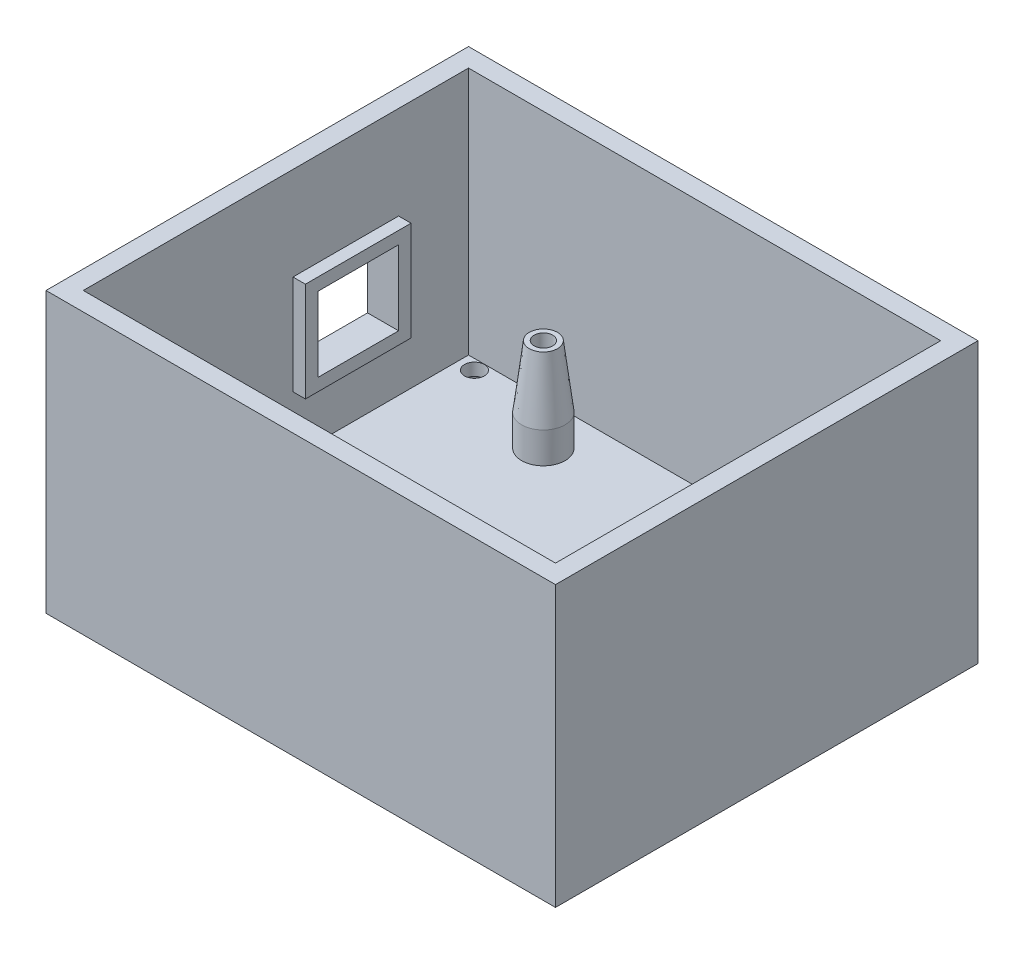
SolidWorks part; units mm, degrees
ref_plane "Спереди" through (0, 0, 0) normal (0, 0, 1) x (1, 0, 0)
ref_plane "Сверху" through (0, 0, 0) normal (0, 1, 0) x (1, 0, 0)
ref_plane "Справа" through (0, 0, 0) normal (1, 0, 0) x (0, 0, -1)
sketch "Sketch1" plane through (0, 0, 0) normal (0, 1, 0) x (1, 0, 0)
  line L1 (41, 34) -> (-41, 34)
  line L2 (41, 34) -> (41, -34)
  line L3 (41, -34) -> (-41, -34)
  line L4 (-41, 34) -> (-41, -34)
  line L5 (41, 34) -> (-41, -34) construction
  line L6 (41, -34) -> (-41, 34) construction
  point P0 (0, 0)
  dimension "D1" = 82
  dimension "D2" = 68
extrude "Boss-Extrude1" add sketch "Sketch1" along normal blind 5
sketch "Sketch2" plane through (0, 5, 0) normal (0, 1, 0) x (1, 0, 0)
  line L1 (-41, 34) -> (41, 34)
  line L2 (-41, 34) -> (-41, -34)
  line L3 (-41, -34) -> (41, -34)
  line L4 (41, 34) -> (41, -34)
  line L5 (-41, 34) -> (41, -34) construction
  line L6 (-41, -34) -> (41, 34) construction
  line L7 (-38, 31) -> (38, 31)
  line L8 (-38, 31) -> (-38, -31)
  line L9 (-38, -31) -> (38, -31)
  line L10 (38, 31) -> (38, -31)
  line L11 (-38, 31) -> (38, -31) construction
  line L12 (-38, -31) -> (38, 31) construction
  point P0 (0, 0)
  point P7 (0, 0)
  dimension "D1" = 3
  dimension "D2" = 3
  dimension "D3" = 76
  dimension "D4" = 62
  dimension "D5" = 82
  dimension "D6" = 68
extrude "Boss-Extrude2" add sketch "Sketch2" along normal blind 40
sketch "Эскиз1" plane through (0, 5, 0) normal (0, 1, 0) x (1, 0, 0)
  line L0 (-34.3, 26.65) -> (34.3, 26.65) construction
  line L1 (34.3, -26.65) -> (-34.3, 26.65) construction
  line L2 (-34.3, -26.65) -> (34.3, 26.65) construction
  line L5 (31.8, -24.15) -> (-34.3, -24.15) construction
  line L7 (34.3, 26.65) -> (34.3, -26.65) construction
  line L8 (34.3, -26.65) -> (-34.3, -26.65) construction
  line L9 (-34.3, -26.65) -> (-34.3, 26.65) construction
  line L10 (-34.3, 26.65) -> (-20.3, 26.65) construction
  line L11 (31.8, 26.65) -> (31.8, 8.85) construction
  line L12 (31.8, 8.85) -> (31.8, 24.05) construction
  line L13 (-20.3, 26.65) -> (-19, 26.65) construction
  line L14 (-20.3, 26.65) -> (-20.3, -26.65) construction
  line L15 (-19, 26.65) -> (31.8, 26.65) construction
  line L16 (31.8, 26.65) -> (31.8, -26.65) construction
  line L17 (31.8, -26.65) -> (31.8, -24.15) construction
  line L18 (31.8, 24.05) -> (-19, 24.05) construction
  line L19 (-19, 26.65) -> (-19, -26.65) construction
  circle A0 centre (31.8, -19.05) radius 1.5
  circle A1 centre (-20.3, -24.15) radius 1.5
  circle A2 centre (31.8, 8.85) radius 1.5
  circle A3 centre (-19, 24.05) radius 1.5
  circle A4 centre (-20.3, -24.15) radius 3.5
  circle A5 centre (-19, 24.05) radius 3.5
  circle A6 centre (31.8, 8.85) radius 3.5
  circle A7 centre (31.8, -19.05) radius 3.5
  point P0 (0, 0)
  point P3 (0, 0)
  point P6 (3.1764, 2.4705)
  point P11 (-20.3, -24.15)
  dimension "D12" = 3
  dimension "D2" = 7
  dimension "D4" = 68.6
  dimension "D5" = 14
  dimension "D6" = 1.3
  dimension "D7" = 50.8
  dimension "D8" = 2.5
  dimension "D9" = 5.1
  dimension "D10" = 27.9
  dimension "D11" = 15.2
extrude "Boss-Extrude3" add sketch "Эскиз1" along normal blind 15
sketch "Sketch4" plane through (-41, 0, 0) normal (-1, 0, 0) x (0, 0, 1)
  line L0 (0, 45) -> (0, 0) construction
  line L1 (-17.75, 28) -> (-4.75, 28)
  line L2 (-17.75, 45) -> (-17.75, 16) construction
  line L3 (-34, 0) -> (34, 0) construction
  line L4 (-4.75, 16) -> (-4.75, 45) construction
  line L5 (26.75, 16) -> (-26.75, 16) construction
  line L6 (-34, 45) -> (34, 45) construction
  line L7 (-17.75, 28) -> (-17.75, 16)
  line L8 (-17.75, 16) -> (-4.75, 16)
  line L10 (-4.75, 16) -> (-4.75, 28)
  point P7 (0, 16)
  point P8 (-11.25, 16)
  dimension "D1" = 53.5
  dimension "D2" = 29
  dimension "D3" = 13
  dimension "D4" = 12
extrude "Cut-Extrude1" cut sketch "Sketch4" against normal up to surface (3 mm away) up to face at (-38, 25, 0)
sketch "Sketch5" plane through (0, 0, 0) normal (0, -1, 0) x (1, 0, 0)
  line L0 (-41, 0) -> (41, 0) construction
  line L1 (-41, -34) -> (-41, 34) construction
  line L2 (41, 34) -> (41, -34) construction
  circle A0 centre (-20, 0) radius 1.6
  circle A1 centre (20, 0) radius 1.6
  dimension "D1" = 40
  dimension "D3" = 3.2
  dimension "D2" = 20
extrude "Cut-Extrude2" cut sketch "Sketch5" against normal through all
sketch "Sketch6" plane through (0, 0, -34) normal (0, 0, -1) x (-1, 0, 0)
  line L0 (-41, 15) -> (41, 15) construction
  line L1 (-41, 45) -> (-41, 0) construction
  line L2 (41, 45) -> (41, 0) construction
  line L3 (-41, 7) -> (41, 7) construction
  line L4 (-41, 0) -> (41, 0) construction
  text T0 "<b>SIMCHAIR MK III</b>" font "Arial Narrow" height 16
  text T1 "<b>I2C EDITION</b>" font "Arial Narrow" height 6
  dimension "D1" = 15
  dimension "D2" = 7
extrude "Boss-Extrude4" add sketch "Sketch6" along normal blind 1
sketch "Sketch7" plane through (0, 0, 0) normal (0, -1, 0) x (1, 0, 0)
  line L0 (-41, -34) -> (41, 34) construction
  line L1 (41, -34) -> (-41, 34) construction
  line L2 (35.4089, -29.3635) -> (-35.4089, -29.3635) construction
  line L3 (-35.4089, -29.3635) -> (-35.4089, 29.3635) construction
  line L4 (-35.4089, 29.3635) -> (35.4089, 29.3635) construction
  line L5 (35.4089, 29.3635) -> (35.4089, -29.3635) construction
  circle A0 centre (35.4089, -29.3635) radius 1.6
  circle A1 centre (-35.4089, -29.3635) radius 1.6
  circle A2 centre (-35.4089, 29.3635) radius 1.6
  circle A3 centre (35.4089, 29.3635) radius 1.6
  dimension "D2" = 3.2
  dimension "D1" = 92
extrude "Cut-Extrude3" cut sketch "Sketch7" against normal through all
sketch "Sketch8" plane through (0, 0, 0) normal (0, -1, 0) x (1, 0, 0)
  line L0 (-41, 34) -> (41, 34) construction
  line L1 (33.7839, 26.5489) -> (37.0339, 26.5489)
  line L2 (37.0339, 26.5489) -> (38.6589, 29.3635)
  line L3 (38.6589, 29.3635) -> (37.0339, 32.178)
  line L4 (37.0339, 32.178) -> (33.7839, 32.178)
  line L5 (33.7839, 32.178) -> (32.1589, 29.3635)
  line L6 (32.1589, 29.3635) -> (33.7839, 26.5489)
  line L7 (33.7839, -26.5489) -> (32.1589, -29.3635)
  line L8 (32.1589, -29.3635) -> (33.7839, -32.178)
  line L9 (33.7839, -32.178) -> (37.0339, -32.178)
  line L10 (37.0339, -32.178) -> (38.6589, -29.3635)
  line L11 (38.6589, -29.3635) -> (37.0339, -26.5489)
  line L12 (37.0339, -26.5489) -> (33.7839, -26.5489)
  line L13 (-37.0339, -26.5489) -> (-38.6589, -29.3635)
  line L14 (-38.6589, -29.3635) -> (-37.0339, -32.178)
  line L15 (-37.0339, -32.178) -> (-33.7839, -32.178)
  line L16 (-33.7839, -32.178) -> (-32.1589, -29.3635)
  line L17 (-32.1589, -29.3635) -> (-33.7839, -26.5489)
  line L18 (-33.7839, -26.5489) -> (-37.0339, -26.5489)
  line L19 (-37.0339, 26.5489) -> (-33.7839, 26.5489)
  line L20 (-33.7839, 26.5489) -> (-32.1589, 29.3635)
  line L21 (-32.1589, 29.3635) -> (-33.7839, 32.178)
  line L22 (-33.7839, 32.178) -> (-37.0339, 32.178)
  line L23 (-37.0339, 32.178) -> (-38.6589, 29.3635)
  line L24 (-38.6589, 29.3635) -> (-37.0339, 26.5489)
  line L25 (41, -34) -> (-41, -34) construction
  circle A0 centre (35.4089, 29.3635) radius 3.25 construction
  circle A1 centre (35.4089, -29.3635) radius 3.25 construction
  circle A2 centre (-35.4089, -29.3635) radius 3.25 construction
  circle A3 centre (-35.4089, 29.3635) radius 3.25 construction
  dimension "D1" = 6.5
extrude "Cut-Extrude4" cut sketch "Sketch8" against normal blind 3
sketch "Sketch10" plane through (-38, 0, 0) normal (1, 0, 0) x (0, 0, -1)
  line L0 (17.75, 28) -> (4.75, 16) construction
  line L2 (4.75, 16) -> (17.75, 16)
  line L3 (4.75, 16) -> (4.75, 28)
  line L4 (4.75, 28) -> (17.75, 28)
  line L5 (17.75, 16) -> (17.75, 28)
  line L6 (4.75, 16) -> (17.75, 28) construction
  line L7 (4.75, 28) -> (17.75, 16) construction
  line L8 (2.75, 14) -> (19.75, 14)
  line L9 (2.75, 14) -> (2.75, 30)
  line L10 (2.75, 30) -> (19.75, 30)
  line L11 (19.75, 14) -> (19.75, 30)
  line L12 (2.75, 14) -> (19.75, 30) construction
  line L13 (2.75, 30) -> (19.75, 14) construction
  point P4 (11.25, 22)
  point P5 (11.25, 22)
  dimension "D1" = 2
  dimension "D2" = 2
extrude "Boss-Extrude6" add sketch "Sketch10" along normal blind 2
chamfer "Chamfer1" distance 10 angle 7 1 edges at (-19, 20, -20.55)
sketch "Sketch11" plane through (0, 5, 0) normal (0, 1, 0) x (1, 0, 0)
  line L0 (-23.25, 0) -> (23.25, 0) construction
  line L1 (-16.75, 0) -> (-18.375, 2.8146)
  line L2 (-18.375, 2.8146) -> (-21.625, 2.8146)
  line L3 (-21.625, 2.8146) -> (-23.25, 0)
  line L4 (-23.25, 0) -> (-21.625, -2.8146)
  line L5 (-21.625, -2.8146) -> (-18.375, -2.8146)
  line L6 (-18.375, -2.8146) -> (-16.75, 0)
  line L7 (16.75, 0) -> (18.375, -2.8146)
  line L8 (18.375, -2.8146) -> (21.625, -2.8146)
  line L9 (21.625, -2.8146) -> (23.25, 0)
  line L10 (23.25, 0) -> (21.625, 2.8146)
  line L11 (21.625, 2.8146) -> (18.375, 2.8146)
  line L12 (18.375, 2.8146) -> (16.75, 0)
  circle A0 centre (-20, 0) radius 3.25 construction
  circle A1 centre (20, 0) radius 3.25 construction
  dimension "D1" = 6.5
extrude "Cut-Extrude5" cut sketch "Sketch11" against normal blind 3
